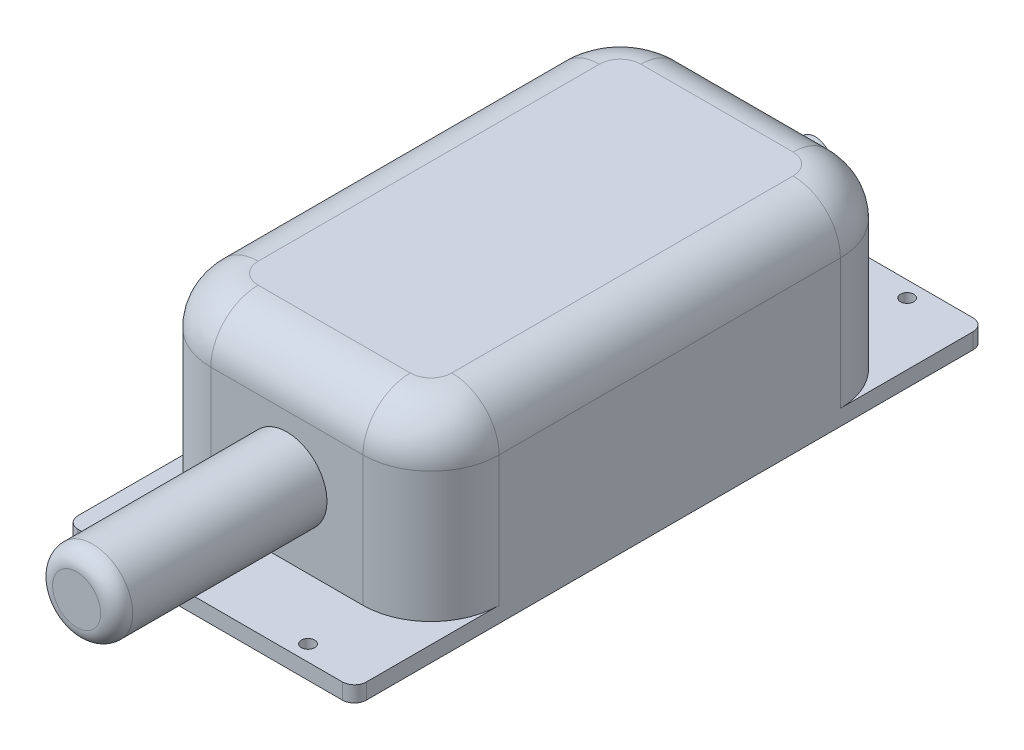
SolidWorks part; units mm, degrees
ref_plane "Front Plane" through (0, 0, 0) normal (0, 0, 1) x (1, 0, 0)
ref_plane "Top Plane" through (0, 0, 0) normal (0, 1, 0) x (1, 0, 0)
ref_plane "Right Plane" through (0, 0, 0) normal (1, 0, 0) x (0, 0, -1)
sketch "Sketch1" plane through (0, 0, 0) normal (0, 1, 0) x (1, 0, 0)
  line L0 (0, -55) -> (0, 55) construction
  line L1 (45.7073, -99.9998) -> (-45.7073, -99.9998)
  line L2 (45.7073, -99.9998) -> (45.7073, 99.9998)
  line L3 (45.7073, 99.9998) -> (-45.7073, 99.9998)
  line L4 (-45.7073, -99.9998) -> (-45.7073, 99.9998)
  line L5 (-55, 0) -> (55, 0) construction
  point P4 (0, -99.9998)
  point P7 (-45.7073, 0)
  dimension "D1" = 199.9996
  dimension "D2" = 91.4146
extrude "Boss-Extrude1" add sketch "Sketch1" along normal blind 5.0038
sketch "Sketch2" plane through (0, 5.0038, 0) normal (0, 1, 0) x (1, 0, 0)
  line L0 (-45.7073, 99.9998) -> (-45.7073, -99.9998) construction
  line L1 (-24.1173, 75.7047) -> (24.1173, 75.7047)
  line L2 (-45.7073, 54.1147) -> (-45.7073, -54.1147)
  line L3 (-24.1173, -75.7047) -> (24.1173, -75.7047)
  line L4 (45.7073, 54.1147) -> (45.7073, -54.1147)
  line L5 (45.7073, -99.9998) -> (45.7073, 99.9998) construction
  line L6 (-2.7521, 0) -> (2.7521, 0) construction
  arc A0 (-45.7073, 54.1147) -> (-24.1173, 75.7047) centre (-24.1173, 54.1147) cw
  arc A1 (24.1173, -75.7047) -> (45.7073, -54.1147) centre (24.1173, -54.1147) ccw
  arc A2 (-45.7073, -54.1147) -> (-24.1173, -75.7047) centre (-24.1173, -54.1147) ccw
  arc A3 (45.7073, 54.1147) -> (24.1173, 75.7047) centre (24.1173, 54.1147) ccw
  point P8 (-45.7073, 0)
  point P13 (-45.7073, 75.7047)
  point P16 (45.7073, -75.7047)
  point P21 (45.7073, 75.7047)
  dimension "D2" = 21.59
  dimension "D1" = 151.4094
extrude "Boss-Extrude2" add sketch "Sketch2" along normal blind 56.3118
fillet "Fillet1" radius 15.0114 8 edges at (-39.3837, 61.3156, -69.3811) (0, 61.3156, -75.7047) (39.3837, 61.3156, -69.3811) (45.7073, 61.3156, 0) (39.3837, 61.3156, 69.3811) (0, 61.3156, 75.7047) (-39.3837, 61.3156, 69.3811) (-45.7073, 61.3156, 0)
sketch "Sketch3" plane through (0, 5.0038, 0) normal (0, 1, 0) x (1, 0, 0)
  line L0 (45.7073, 99.9998) -> (-45.7073, 99.9998) construction
  line L3 (45.7073, 54.1147) -> (45.7073, 99.9998) construction
  line L4 (0, 99.9998) -> (0, -99.9998) construction
  line L5 (-45.7073, -99.9998) -> (45.7073, -99.9998) construction
  line L7 (-45.7073, 0) -> (45.7073, 0) construction
  line L8 (-45.7073, 99.9998) -> (-45.7073, -99.9998) construction
  line L9 (45.7073, -99.9998) -> (45.7073, 99.9998) construction
  circle A0 centre (25.9969, 94.996) radius 2.1082
  circle A1 centre (-25.9969, 94.996) radius 2.1082
  circle A2 centre (25.9969, -94.996) radius 2.1082
  circle A3 centre (-25.9969, -94.996) radius 2.1082
  point P7 (0, 0)
  point P17 (-45.7073, 0)
  point P18 (0, 0)
  point P21 (45.7073, 0)
  dimension "D1" = 4.2164
  dimension "D2" = 5.0038
  dimension "D3" = 19.7104
extrude "Cut-Extrude1" cut sketch "Sketch3" against normal up to next
fillet "Fillet2" radius 3.81 4 edges at (-45.7073, 2.5019, 99.9998) (45.7073, 2.5019, 99.9998) (-45.7073, 2.5019, -99.9998) (45.7073, 2.5019, -99.9998)
sketch "Sketch5" plane through (0, 0, 75.7047) normal (0, 0, 1) x (1, 0, 0)
  line L0 (0, -33.7236) -> (0, 33.7236) construction
  line L1 (-24.1173, 5.0038) -> (24.1173, 5.0038) construction
  circle A0 centre (0, 27.8638) radius 12.7
  point P2 (-5.8405, 29.119)
  point P5 (0, 0)
  dimension "D1" = 25.4
  dimension "D2" = 22.86
extrude "Boss-Extrude3" add sketch "Sketch5" along normal blind 66.675
fillet "Fillet3" radius 5.08 1 edges at (12.7, 27.8638, 142.3797)
sketch "Sketch6" plane through (0, 0, -75.7047) normal (0, 0, -1) x (-1, 0, 0)
  line L0 (0, 33.7236) -> (0, -33.7236) construction
  circle A0 centre (0, 32.2698) radius 5.588
  point P2 (0, 0)
extrude "Boss-Extrude4" add sketch "Sketch6" along normal blind 16.1544
